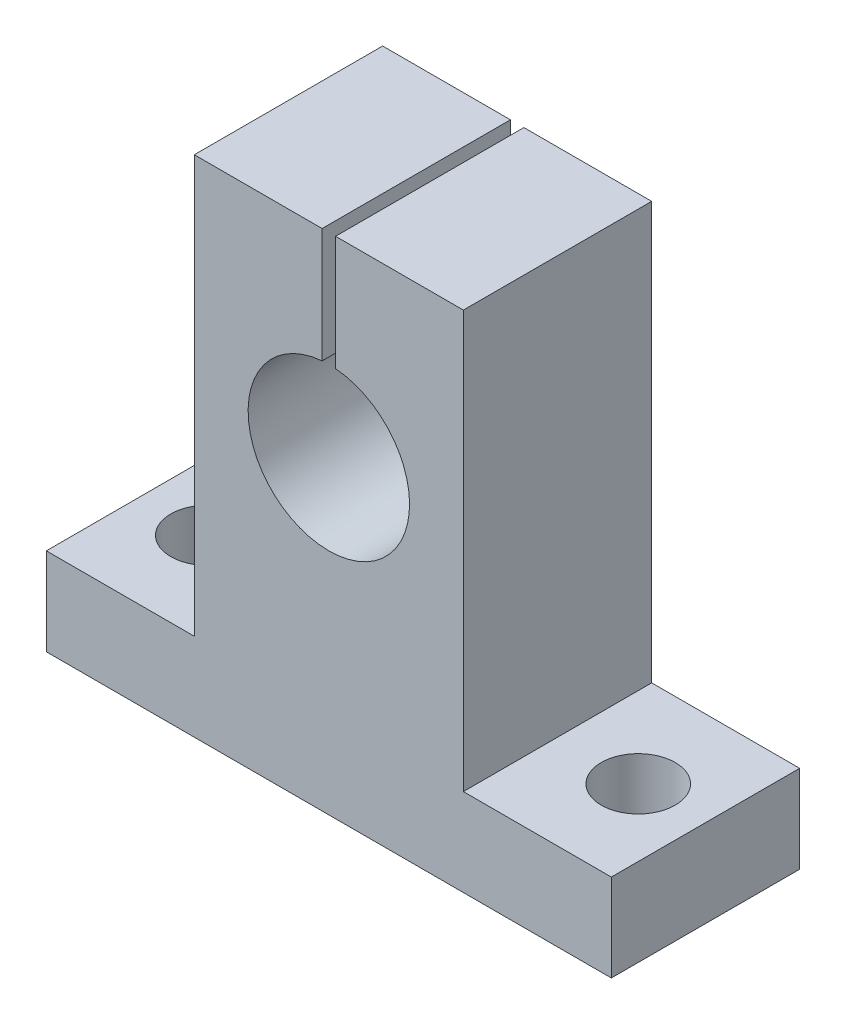
SolidWorks part; units mm, degrees
ref_plane "Ön Düzlem" through (0, 0, 0) normal (0, 0, 1) x (1, 0, 0)
ref_plane "Üst Düzlem" through (0, 0, 0) normal (0, 1, 0) x (1, 0, 0)
ref_plane "Sağ Düzlem" through (0, 0, 0) normal (1, 0, 0) x (0, 0, -1)
sketch "Çizim1" plane through (0, 0, 0) normal (0, 0, 1) x (1, 0, 0)
  line L0 (0, 66.7408) -> (0, -66.7408) construction
  line L1 (21, -23) -> (-21, -23)
  line L2 (-21, -23) -> (-21, -16.5)
  line L3 (-21, -16.5) -> (-10, -16.5)
  line L4 (-10, -16.5) -> (-10, 14.5)
  line L5 (-10, 14.5) -> (-0.5, 14.5)
  line L6 (-0.5, 14.5) -> (-0.5, 5.9791)
  line L7 (0.5, 14.5) -> (0.5, 5.9791)
  line L8 (10, 14.5) -> (0.5, 14.5)
  line L9 (10, -16.5) -> (10, 14.5)
  line L10 (21, -16.5) -> (10, -16.5)
  line L11 (21, -23) -> (21, -16.5)
  arc A0 (-0.5, 5.9791) -> (0.5, 5.9791) centre (0, 0) ccw
  point P18 (0, -23)
  dimension "D3" = 12
  dimension "D1" = 23
  dimension "D2" = 21
  dimension "D4" = 37.5
  dimension "D5" = 6.5
  dimension "D6" = 10
  dimension "D7" = 9.5
extrude "Yükseklik-Ekstrüzyon2" add sketch "Çizim1" along normal blind 14 contours L4 L5 L6 A0 L7 L8 L9 L10 L11 L1 L2 L3
sketch "Çizim2" plane through (0, -23, 0) normal (0, -1, 0) x (1, 0, 0)
  line L0 (0, 14) -> (0, 0) construction
  line L1 (21, 14) -> (-21, 14) construction
  line L2 (21, 0) -> (-21, 0) construction
  circle A0 centre (-16, 7) radius 2.75
  circle A1 centre (16, 7) radius 2.75
  point P10 (0, 7)
  point P11 (0, 0)
  point P13 (-14.9599, 7)
  dimension "D3" = 5.5
  dimension "D1" = 32
  dimension "D2" = 16
extrude "Kes-Ekstrüzyon1" cut sketch "Çizim2" against normal up to next and the other way through all
